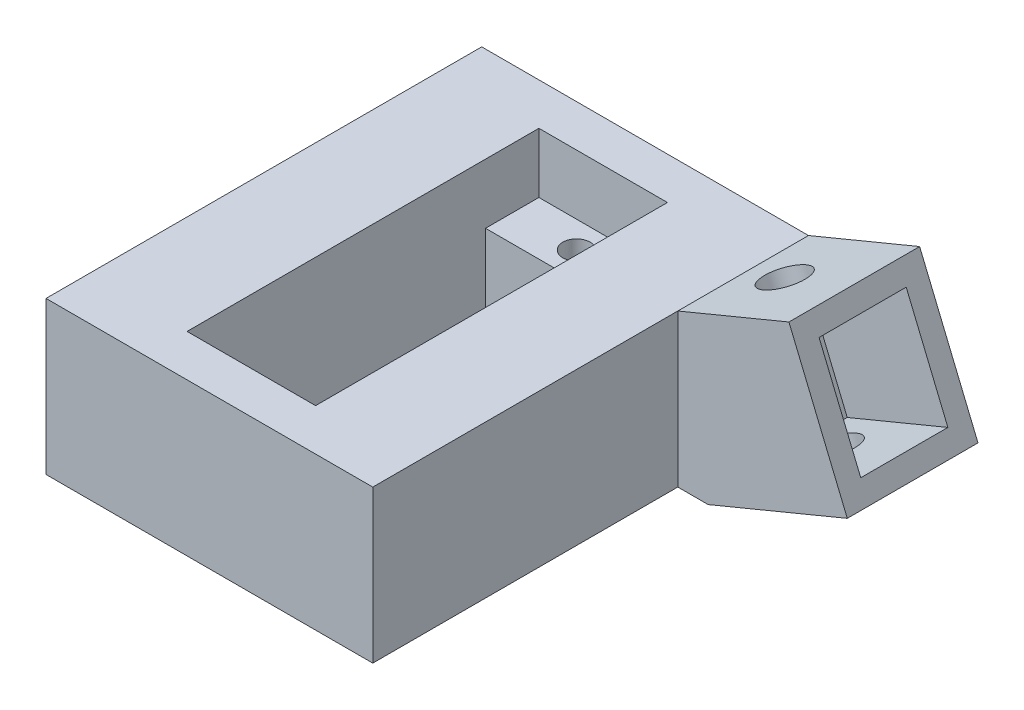
SolidWorks part; units mm, degrees
ref_plane "Front Plane" through (0, 0, 0) normal (0, 0, 1) x (1, 0, 0)
ref_plane "Top Plane" through (0, 0, 0) normal (0, 1, 0) x (1, 0, 0)
ref_plane "Right Plane" through (0, 0, 0) normal (1, 0, 0) x (0, 0, -1)
sketch "Sketch1" plane through (0, 0, 0) normal (0, 0, 1) x (1, 0, 0)
  line L1 (8.671, 9.0036) -> (-11.329, 9.0036)
  line L3 (11.4585, -4.9953) -> (8.671, -4.9953)
  line L5 (-11.329, -4.9953) -> (8.671, -4.9953)
  line L9 (8.671, 9.0036) -> (8.671, -4.9953)
  line L15 (-11.329, 9.0036) -> (-21.329, 9.0036)
  line L17 (-21.329, 9.0036) -> (-21.329, -4.9953)
  line L18 (-21.329, -4.9953) -> (-11.329, -4.9953)
  line L25 (18.8739, 13.2298) -> (8.671, 9.0036)
  line L26 (20.7873, 8.6104) -> (18.8739, 13.2298)
  line L27 (24.2314, 0.2955) -> (11.4585, -4.9953)
  line L28 (20.7873, 8.6104) -> (24.2314, 0.2955)
  dimension "D1" = 20
extrude "Boss-Extrude1" add sketch "Sketch1" along normal blind 40 contours L1 L15 L17 L18 L5 L9
sketch "Sketch3" plane through (0, 9.0036, 0) normal (0, 1, 0) x (1, 0, 0)
  line L0 (-6.329, -40) -> (-6.329, 0) construction
  line L1 (8.671, -40) -> (-21.329, -40) construction
  line L2 (-11.329, 0) -> (8.671, 0) construction
  line L3 (-21.329, -20) -> (8.671, -20) construction
  line L4 (-21.329, -40) -> (-21.329, 0) construction
  line L5 (8.671, -40) -> (8.671, 0) construction
  line L6 (-12.229, -31.25) -> (-0.429, -31.25)
  line L8 (-12.229, -3.85) -> (-12.229, -36.15)
  line L9 (-12.229, -36.15) -> (-0.429, -36.15)
  line L10 (-0.429, -3.85) -> (-0.429, -36.15)
  line L11 (-6.329, -31.25) -> (-6.329, -36.15) construction
  line L12 (-12.229, -3.85) -> (-0.429, -3.85)
  line L13 (-12.229, -8.75) -> (-0.429, -8.75)
  circle A0 centre (-6.329, -33.7) radius 1.25
  circle A1 centre (-6.329, -6.3) radius 1.25
  point P24 (-0.429, -20)
  point P26 (-12.229, -20)
  dimension "D1" = 11.8
  dimension "D2" = 5.9
  dimension "D3" = 16.15
  dimension "D4" = 4.9
sketch "Sketch4" plane through (0, 9.0036, 0) normal (0, 1, 0) x (1, 0, 0)
  line L0 (-12.229, -36.15) -> (-0.429, -36.15) construction
  line L1 (-0.429, -3.85) -> (-0.429, -36.15) construction
  line L2 (-12.229, -3.85) -> (-0.429, -3.85) construction
  line L3 (-12.229, -3.85) -> (-12.229, -36.15) construction
  line L4 (-12.229, -36.15) -> (-0.429, -36.15)
  line L5 (-0.429, -3.85) -> (-0.429, -36.15)
  line L6 (-12.229, -3.85) -> (-0.429, -3.85)
  line L7 (-12.229, -3.85) -> (-12.229, -36.15)
extrude "Cut-Extrude1" cut sketch "Sketch4" against normal blind 5.5
sketch "Sketch5" plane through (0, 3.5036, 0) normal (0, 1, 0) x (1, 0, 0)
  line L0 (-12.229, -31.25) -> (-0.429, -31.25) construction
  line L1 (-0.429, -3.85) -> (-0.429, -36.15) construction
  line L2 (-12.229, -3.85) -> (-12.229, -36.15) construction
  line L3 (-12.229, -8.75) -> (-0.429, -8.75) construction
  line L4 (-12.229, -31.25) -> (-0.429, -31.25)
  line L5 (-0.429, -8.75) -> (-0.429, -31.25)
  line L6 (-12.229, -8.75) -> (-12.229, -31.25)
  line L7 (-12.229, -8.75) -> (-0.429, -8.75)
extrude "Cut-Extrude2" cut sketch "Sketch5" against normal through all
sketch "Sketch6" plane through (0, 3.5036, 0) normal (0, 1, 0) x (1, 0, 0)
  circle A0 centre (-6.329, -6.3) radius 1.25
  circle A1 centre (-6.329, -33.7) radius 1.25
extrude "Cut-Extrude3" cut sketch "Sketch6" against normal through all
sketch "Sketch7" plane through (0, 0, 0) normal (0, 0, 1) x (1, 0, 0)
  line L0 (8.671, 9.0036) -> (8.671, -4.9953) construction
  line L1 (11.4585, -4.9953) -> (8.671, -4.9953) construction
  line L2 (24.2314, 0.2955) -> (11.4585, -4.9953) construction
  line L3 (20.7873, 8.6104) -> (24.2314, 0.2955) construction
  line L4 (18.8739, 13.2298) -> (8.671, 9.0036) construction
  line L5 (20.7873, 8.6104) -> (18.8739, 13.2298) construction
  line L6 (8.671, 9.0036) -> (8.671, -4.9953)
  line L7 (11.4585, -4.9953) -> (8.671, -4.9953)
  line L8 (24.2314, 0.2955) -> (11.4585, -4.9953)
  line L9 (20.7873, 8.6104) -> (24.2314, 0.2955)
  line L10 (18.8739, 13.2298) -> (8.671, 9.0036)
  line L11 (20.7873, 8.6104) -> (18.8739, 13.2298)
extrude "Boss-Extrude2" add sketch "Sketch7" along normal blind 12
sketch "Sketch8" plane through (20.7873, 8.6104, 0) normal (0.9239, 0.3827, 0) x (0, 0, -1)
  line L0 (-12, 5) -> (0, 5) construction
  line L1 (-10, 3) -> (-2, 3)
  line L2 (-10, 3) -> (-10, -7)
  line L3 (-10, -7) -> (-2, -7)
  line L4 (-2, 3) -> (-2, -7)
  line L5 (-12, -9) -> (0, -9) construction
  line L6 (0, -9) -> (0, 5) construction
  line L7 (-12, -9) -> (-12, 5) construction
  point P8 (-2, -2)
  dimension "D1" = 2
  dimension "D2" = 2
  dimension "D3" = 2
  dimension "D4" = 2
extrude "Cut-Extrude4" cut sketch "Sketch8" against normal blind 10
sketch "Sketch9" plane through (3.4442, -8.3149, 0) normal (0.3827, -0.9239, 0) x (0.9239, 0.3827, 0)
  line L0 (8.6747, 6) -> (22.5, 6) construction
  line L1 (8.6747, 12) -> (8.6747, 0) construction
  line L2 (22.5, 12) -> (22.5, 0) construction
  line L3 (15.5873, 0) -> (15.5873, 12) construction
  line L4 (8.6747, 0) -> (22.5, 0) construction
  line L5 (8.6747, 12) -> (22.5, 12) construction
  circle A0 centre (15.5873, 6) radius 2
extrude "Cut-Extrude5" cut sketch "Sketch9" against normal through all
